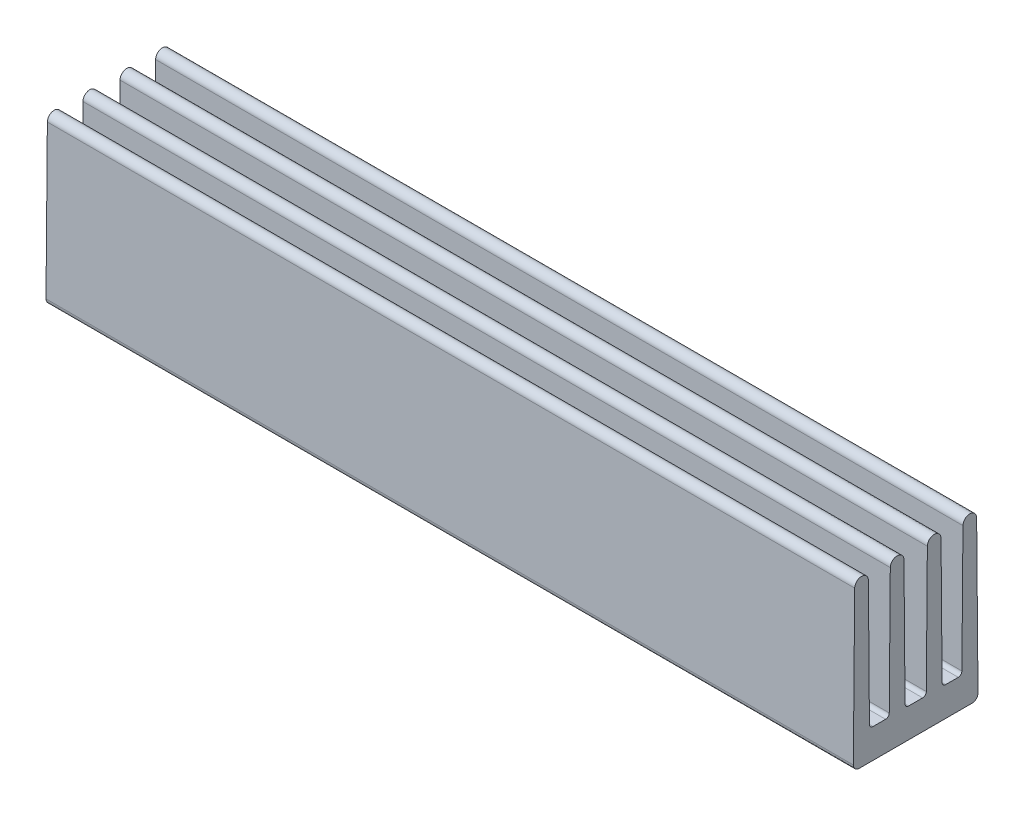
SolidWorks part; units mm, degrees
ref_plane "Front" through (0, 0, 0) normal (0, 0, 1) x (1, 0, 0)
ref_plane "Top" through (0, 0, 0) normal (0, 1, 0) x (1, 0, 0)
ref_plane "Right" through (0, 0, 0) normal (1, 0, 0) x (0, 0, -1)
sketch "Sketch1" plane through (0, 0, 0) normal (1, 0, 0) x (0, 0, -1)
  line L0 (-4.15, 11.25) -> (-4.25, 0)
  line L1 (-4.25, 0) -> (4.25, 0)
  line L2 (4.25, 0) -> (4.15, 11.25)
  line L3 (4.15, 11.25) -> (-4.15, 11.25)
  line L4 (0, 0) -> (0, 14.2764) construction
  dimension "D1" = 11.25
  dimension "D2" = 8.5
  dimension "D3" = 8.3
extrude "Boss-Extrude1" add sketch "Sketch1" along normal mid plane 55
sketch "Sketch2" plane through (27.5, 0, 0) normal (1, 0, 0) x (0, 0, -1)
  line L0 (0, 12.4606) -> (0, 0) construction
  line L1 (-0.8, 11.25) -> (-0.725, 2.2479)
  line L2 (4.15, 11.25) -> (-4.15, 11.25) construction
  line L3 (-0.475, 2) -> (0.475, 2)
  line L4 (0.725, 2.2479) -> (0.8, 11.25)
  line L5 (0.8, 11.25) -> (-0.8, 11.25)
  line L6 (-3.225, 11.25) -> (-1.725, 11.25)
  line L7 (-1.725, 11.25) -> (-1.8, 2.2479)
  line L8 (-2.05, 2) -> (-2.9, 2)
  line L9 (-3.15, 2.2479) -> (-3.225, 11.25)
  line L10 (-2.475, 11.25) -> (-2.475, 2) construction
  line L11 (3.225, 11.25) -> (1.725, 11.25)
  line L12 (3.15, 2.2479) -> (3.225, 11.25)
  line L13 (2.05, 2) -> (2.9, 2)
  line L14 (1.725, 11.25) -> (1.8, 2.2479)
  line L15 (-4.15, 11.25) -> (-3.225, 11.25) construction
  line L16 (-1.725, 11.25) -> (-0.8, 11.25) construction
  line L17 (0.8, 11.25) -> (1.725, 11.25) construction
  arc A0 (-0.725, 2.2479) -> (-0.475, 2) centre (-0.475, 2.25) ccw
  arc A1 (0.475, 2) -> (0.725, 2.2479) centre (0.475, 2.25) ccw
  arc A2 (-1.8, 2.2479) -> (-2.05, 2) centre (-2.05, 2.25) cw
  arc A3 (-2.9, 2) -> (-3.15, 2.2479) centre (-2.9, 2.25) cw
  arc A4 (2.9, 2) -> (3.15, 2.2479) centre (2.9, 2.25) ccw
  arc A5 (1.8, 2.2479) -> (2.05, 2) centre (2.05, 2.25) ccw
  dimension "D3" = 0.25
  dimension "D1" = 9.25
  dimension "D2" = 1.6
  dimension "D4" = 1.45
  dimension "D5" = 1.5
extrude "Cut-Extrude1" cut sketch "Sketch2" against normal through all
fillet "Fillet1" radius 0.4665 4 edges at (-27.5, 11.25, 3.6875) (27.5, 11.25, 3.6875) (0, 11.25, 3.225) (0, 11.25, 4.15)
fillet "Fillet2" radius 0.4664 4 edges at (-27.5, 11.25, 1.2625) (27.5, 11.25, 1.2625) (0, 11.25, 0.8) (0, 11.25, 1.725)
fillet "Fillet3" radius 0.4664 4 edges at (0, 11.25, -0.8) (-27.5, 11.25, -1.2625) (27.5, 11.25, -1.2625) (0, 11.25, -1.725)
fillet "Fillet4" radius 0.4665 4 edges at (27.5, 11.25, -3.6875) (-27.5, 11.25, -3.6875) (0, 11.25, -3.225) (0, 11.25, -4.15)
fillet "Fillet5" radius 0.4 2 edges at (0, 0, -4.25) (0, 0, 4.25)
